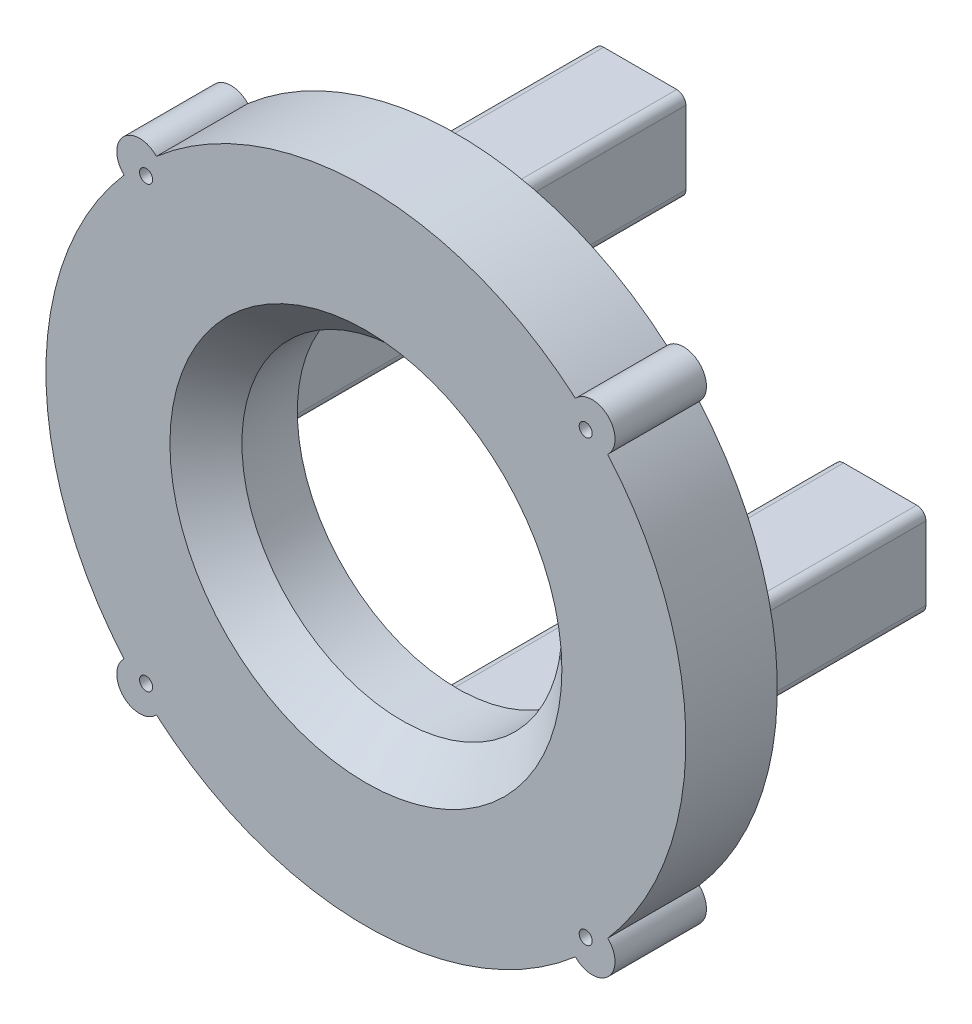
SolidWorks part; units mm, degrees
material "6061-T6 (SS)"
ref_plane "Front Plane" through (0, 0, 0) normal (0, 0, 1) x (1, 0, 0)
ref_plane "Top Plane" through (0, 0, 0) normal (0, 1, 0) x (1, 0, 0)
ref_plane "Right Plane" through (0, 0, 0) normal (1, 0, 0) x (0, 0, -1)
sketch "Sketch1" plane through (0, 0, 0) normal (0, 0, 1) x (1, 0, 0)
  line L0 (0, 0) -> (88.9, 0) construction
  line L1 (0, 0) -> (62.8618, 62.8618) construction
  line L2 (0, 0) -> (85.8708, -23.009) construction
  line L3 (0, 0) -> (23.009, -85.8708) construction
  line L4 (0, 0) -> (-62.8618, -62.8618) construction
  line L5 (0, 0) -> (-85.8708, 23.009) construction
  line L6 (0, 0) -> (-23.009, 85.8708) construction
  circle A0 centre (0, 0) radius 88.9
  circle A1 centre (0, 0) radius 44.45
  circle A13 centre (62.8618, 62.8618) radius 6.35
  circle A14 centre (62.8618, -62.8618) radius 6.35
  circle A15 centre (0, 0) radius 88.9
  circle A16 centre (-62.8618, -62.8618) radius 6.35
  circle A17 centre (0, 0) radius 88.9
  circle A18 centre (-62.8618, 62.8618) radius 6.35
  circle A19 centre (0, 0) radius 88.9
  point P14 (0, 0)
  point P20 (0, 0)
  point P36 (0, 0)
  dimension "D1" = 177.8
  dimension "D2" = 88.9
  dimension "D5" = 4
  dimension "D3" = 45
  dimension "D4" = 6
extrude "Boss-Extrude1" add sketch "Sketch1" along normal blind 25.4
chamfer "Chamfer1" distance 10 angle 45 1 edges at (44.45, 0, 25.4)
sketch "Sketch3" plane through (0, 0, 25.4) normal (0, 0, 1) x (1, 0, 0)
  line L0 (0, 0) -> (61.0657, 61.0657) construction
  line L1 (0, 0) -> (86.36, 0) construction
  circle A7 centre (0, 0) radius 86.36
  circle A15 centre (61.0657, 61.0657) radius 1.8161
  circle A16 centre (61.0657, -61.0657) radius 1.8161
  circle A17 centre (0, 0) radius 86.36
  circle A18 centre (-61.0657, -61.0657) radius 1.8161
  circle A19 centre (0, 0) radius 86.36
  circle A20 centre (-61.0657, 61.0657) radius 1.8161
  circle A21 centre (0, 0) radius 86.36
  point P15 (0, 0)
  point P17 (0, 0)
  point P20 (0, 0)
  dimension "D1" = 172.72
  dimension "D3" = 4
  dimension "D4" = 3.6322
  dimension "D2" = 45
extrude "Cut-Extrude1" cut sketch "Sketch3" against normal through all contours A19 A20 | A19 A20 | A7 A15 | A7 A15 | A7 A16 | A7 A16 | A17 A18 | A17 A18
sketch "Sketch5" plane through (0, 0, 0) normal (0, 0, -1) x (-1, 0, 0)
  line L0 (-67.3519, -67.3519) -> (67.3519, 67.3519) construction
  line L1 (67.3519, -67.3519) -> (-67.3519, 67.3519) construction
  line L2 (0, -58.3285) -> (0, 0) construction
  line L3 (-58.3285, 0) -> (0, 0) construction
  line L4 (0, 58.3285) -> (0, 0) construction
  line L5 (58.3285, 0) -> (0, 0) construction
  line L6 (-76.835, 12.7) -> (-56.515, 12.7)
  line L15 (-10.16, -79.375) -> (10.16, -79.375)
  line L16 (-12.7, -76.835) -> (-12.7, -56.515)
  line L17 (-10.16, -53.975) -> (10.16, -53.975)
  line L18 (12.7, -76.835) -> (12.7, -56.515)
  line L19 (-12.7, -79.375) -> (12.7, -53.975) construction
  line L20 (-12.7, -53.975) -> (12.7, -79.375) construction
  line L21 (-79.375, 10.16) -> (-79.375, -10.16)
  line L22 (-76.835, -12.7) -> (-56.515, -12.7)
  line L23 (-53.975, 10.16) -> (-53.975, -10.16)
  line L24 (12.7, 76.835) -> (12.7, 56.515)
  line L25 (10.16, 79.375) -> (-10.16, 79.375)
  line L26 (-12.7, 76.835) -> (-12.7, 56.515)
  line L27 (10.16, 53.975) -> (-10.16, 53.975)
  line L28 (76.835, -12.7) -> (56.515, -12.7)
  line L29 (79.375, -10.16) -> (79.375, 10.16)
  line L30 (76.835, 12.7) -> (56.515, 12.7)
  line L31 (53.975, -10.16) -> (53.975, 10.16)
  arc A0 (-67.1887, -58.2142) -> (-58.2142, -67.1887) centre (-62.8618, -62.8618) ccw construction
  arc A1 (67.1887, 58.2142) -> (58.2142, 67.1887) centre (62.8618, 62.8618) ccw construction
  arc A2 (58.2142, -67.1887) -> (67.1887, -58.2142) centre (62.8618, -62.8618) ccw construction
  arc A3 (-58.2142, 67.1887) -> (-67.1887, 58.2142) centre (-62.8618, 62.8618) ccw construction
  arc A4 (10.16, -79.375) -> (12.7, -76.835) centre (10.16, -76.835) ccw
  arc A5 (-10.16, -53.975) -> (-12.7, -56.515) centre (-10.16, -56.515) ccw
  arc A6 (-12.7, -76.835) -> (-10.16, -79.375) centre (-10.16, -76.835) ccw
  arc A7 (12.7, -56.515) -> (10.16, -53.975) centre (10.16, -56.515) ccw
  arc A8 (-76.835, 12.7) -> (-79.375, 10.16) centre (-76.835, 10.16) ccw
  arc A9 (-53.975, 10.16) -> (-56.515, 12.7) centre (-56.515, 10.16) ccw
  arc A10 (-79.375, -10.16) -> (-76.835, -12.7) centre (-76.835, -10.16) ccw
  arc A11 (-56.515, -12.7) -> (-53.975, -10.16) centre (-56.515, -10.16) ccw
  arc A12 (12.7, 76.835) -> (10.16, 79.375) centre (10.16, 76.835) ccw
  arc A13 (10.16, 53.975) -> (12.7, 56.515) centre (10.16, 56.515) ccw
  arc A14 (-10.16, 79.375) -> (-12.7, 76.835) centre (-10.16, 76.835) ccw
  arc A15 (-12.7, 56.515) -> (-10.16, 53.975) centre (-10.16, 56.515) ccw
  arc A16 (76.835, -12.7) -> (79.375, -10.16) centre (76.835, -10.16) ccw
  arc A17 (53.975, -10.16) -> (56.515, -12.7) centre (56.515, -10.16) ccw
  arc A18 (79.375, 10.16) -> (76.835, 12.7) centre (76.835, 10.16) ccw
  arc A19 (56.515, 12.7) -> (53.975, 10.16) centre (56.515, 10.16) ccw
  point P18 (0, -66.675)
  point P19 (0, -66.675)
  point P24 (0, 0)
  point P79 (0, 0)
  dimension "D4" = 25.4
  dimension "D6" = 2.54
  dimension "D1" = 45
  dimension "D3" = 66.675
  dimension "D5" = 25.4
  dimension "D2" = 4
  dimension "D7" = 4
extrude "Boss-Extrude3" add sketch "Sketch5" along normal blind 50.8
